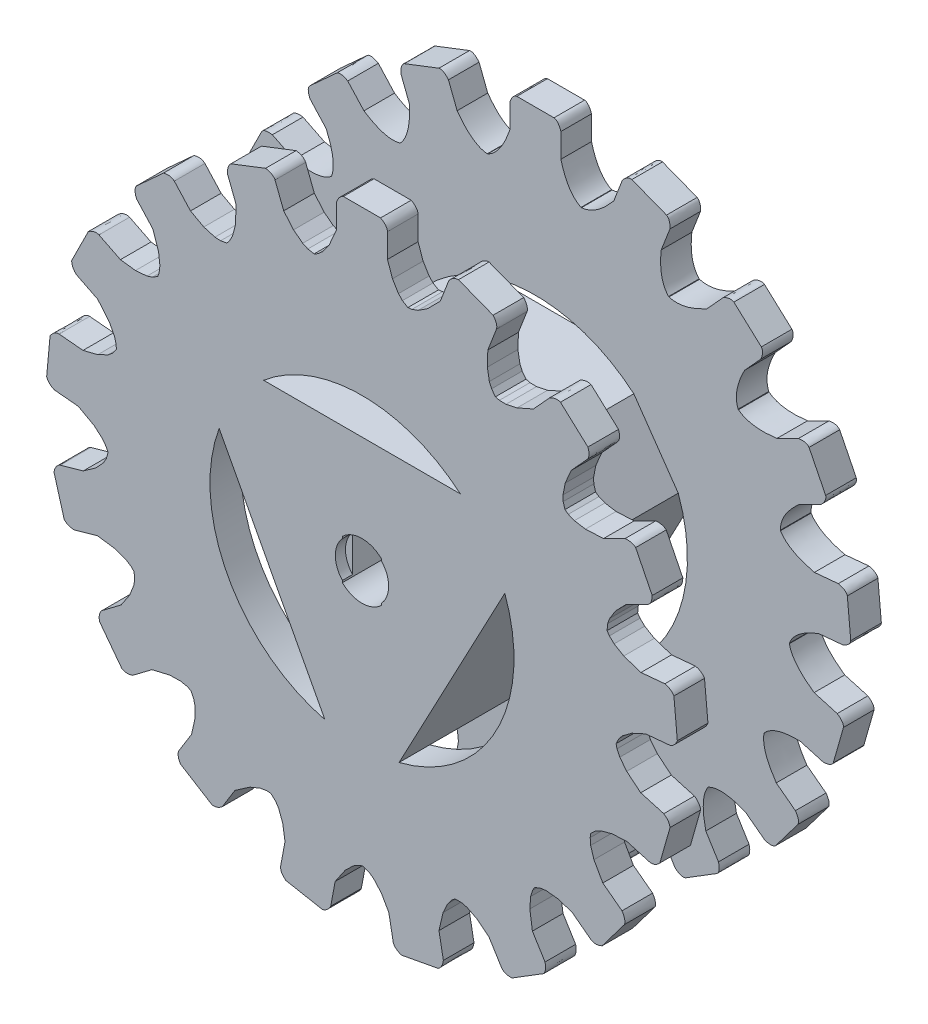
SolidWorks part; units mm, degrees
ref_plane "Front Plane" through (0, 0, 0) normal (0, 0, 1) x (1, 0, 0)
ref_plane "Top Plane" through (0, 0, 0) normal (0, 1, 0) x (1, 0, 0)
ref_plane "Right Plane" through (0, 0, 0) normal (1, 0, 0) x (0, 0, -1)
sketch "Sketch1" plane through (0, 0, 0) normal (0, 0, 1) x (1, 0, 0)
  line L0 (8.5238, 28.923) -> (7.6731, 26.7272)
  line L1 (-1.8223, 30.8747) -> (1.8223, 30.8747)
  line L2 (-2.5, 30.049) -> (-2.5, 27.6942)
  line L4 (2.5, 30.049) -> (2.5, 27.6942)
  line L5 (9.4539, 29.4481) -> (12.8525, 28.1315)
  line L6 (13.1861, 27.1167) -> (12.3355, 24.921)
  line L7 (18.3964, 23.8907) -> (16.8099, 22.1505)
  line L8 (19.4534, 24.0444) -> (22.1469, 21.589)
  line L9 (22.0914, 20.5222) -> (20.505, 18.782)
  line L10 (25.7844, 15.6319) -> (23.6765, 14.5823)
  line L11 (26.8256, 15.3933) -> (28.4502, 12.1307)
  line L12 (28.0131, 11.1561) -> (25.9052, 10.1065)
  line L13 (29.6901, 5.2619) -> (27.3454, 5.0446)
  line L14 (30.5748, 4.6633) -> (30.9111, 1.0342)
  line L15 (30.1515, 0.2832) -> (27.8067, 0.066)
  line L16 (29.5861, -5.8187) -> (27.3211, -5.1743)
  line L17 (30.1948, -6.6965) -> (29.1974, -10.202)
  line L18 (28.2177, -10.6279) -> (25.9528, -9.9834)
  line L19 (25.4862, -16.1135) -> (23.607, -14.6944)
  line L20 (25.7367, -17.1519) -> (23.5403, -20.0604)
  line L21 (22.473, -20.1036) -> (20.5939, -18.6845)
  line L22 (17.9443, -24.2321) -> (16.7047, -22.23)
  line L23 (17.8028, -25.2908) -> (14.704, -27.2095)
  line L24 (13.6932, -26.8643) -> (12.4536, -24.8622)
  line L25 (7.9789, -29.078) -> (7.5462, -26.7633)
  line L26 (7.4645, -30.0141) -> (3.8819, -30.6838)
  line L27 (3.0641, -29.9967) -> (2.6314, -27.682)
  line L28 (-3.0641, -29.9967) -> (-2.6314, -27.682)
  line L29 (-3.8819, -30.6838) -> (-7.4645, -30.0141)
  line L30 (-7.9789, -29.078) -> (-7.5462, -26.7633)
  line L31 (-13.6932, -26.8643) -> (-12.4536, -24.8622)
  line L32 (-14.704, -27.2095) -> (-17.8028, -25.2908)
  line L33 (-17.9443, -24.2321) -> (-16.7047, -22.23)
  line L34 (-22.473, -20.1036) -> (-20.5939, -18.6845)
  line L35 (-23.5403, -20.0604) -> (-25.7367, -17.1519)
  line L36 (-25.4862, -16.1135) -> (-23.607, -14.6944)
  line L37 (-28.2177, -10.6279) -> (-25.9528, -9.9834)
  line L38 (-29.1974, -10.202) -> (-30.1948, -6.6965)
  line L39 (-29.5861, -5.8187) -> (-27.3211, -5.1743)
  line L40 (-30.1515, 0.2832) -> (-27.8067, 0.066)
  line L41 (-30.9111, 1.0342) -> (-30.5748, 4.6633)
  line L42 (-29.6901, 5.2619) -> (-27.3454, 5.0446)
  line L43 (-28.0131, 11.1561) -> (-25.9052, 10.1065)
  line L44 (-28.4502, 12.1307) -> (-26.8256, 15.3933)
  line L45 (-25.7844, 15.6319) -> (-23.6765, 14.5823)
  line L46 (-22.0914, 20.5222) -> (-20.505, 18.782)
  line L47 (-22.1469, 21.589) -> (-19.4534, 24.0444)
  line L48 (-18.3964, 23.8907) -> (-16.8099, 22.1505)
  line L49 (-13.1861, 27.1167) -> (-12.3355, 24.921)
  line L50 (-12.8525, 28.1315) -> (-9.4539, 29.4481)
  line L51 (-8.5238, 28.923) -> (-7.6731, 26.7272)
  line L52 (3.6345, -14.4507) -> (14.0017, 5.0974)
  line L55 (-9.6443, 11.3587) -> (9.6443, 11.3587)
  line L59 (-14.0017, 5.0974) -> (-3.6345, -14.4507)
  arc A0 (-4.6728, 24.5594) -> (-4.7171, 24.5509) centre (0, 0) ccw
  arc A1 (-13.2291, 21.213) -> (-13.2674, 21.1891) centre (0, 0) ccw
  arc A2 (4.5146, 24.589) -> (4.4702, 24.5971) centre (0, 0) ccw
  arc A3 (13.0923, 21.2977) -> (13.0539, 21.3213) centre (0, 0) ccw
  arc A4 (19.9018, 15.13) -> (19.8745, 15.1659) centre (0, 0) ccw
  arc A5 (-19.9988, 15.0016) -> (-20.0259, 14.9655) centre (0, 0) ccw
  arc A6 (-24.0675, 6.7642) -> (-24.0797, 6.7207) centre (0, 0) ccw
  arc A7 (-24.8858, -2.3868) -> (-24.8815, -2.4317) centre (0, 0) ccw
  arc A8 (24.0235, 6.9189) -> (24.011, 6.9623) centre (0, 0) ccw
  arc A9 (24.9006, -2.2266) -> (24.9046, -2.1816) centre (0, 0) ccw
  arc A10 (22.4148, -11.0714) -> (22.4348, -11.0309) centre (0, 0) ccw
  arc A11 (16.9018, -18.4209) -> (16.935, -18.3904) centre (0, 0) ccw
  arc A12 (9.106, -23.2826) -> (9.148, -23.2662) centre (0, 0) ccw
  arc A13 (0.0804, -24.9999) -> (0.1256, -24.9997) centre (0, 0) ccw
  arc A14 (-8.956, -23.3407) -> (-8.9138, -23.3569) centre (0, 0) ccw
  arc A15 (-16.7829, -18.5293) -> (-16.7494, -18.5596) centre (0, 0) ccw
  arc A16 (-22.3431, -11.2154) -> (-22.3228, -11.2557) centre (0, 0) ccw
  arc A17 (3.6345, -14.4507) -> (14.0017, 5.0974) centre (0, 0) ccw
  arc A18 (-14.0017, 5.0974) -> (-3.6345, -14.4507) centre (0, 0) ccw
  arc A19 (9.6443, 11.3587) -> (-9.6443, 11.3587) centre (0, 0) ccw
  spline S0 degree 2 poles (-2.5, 27.6942) (-3.35, 25.1957) (-4.6728, 24.5594) knots 0 0 0 0.372776 0.372776 0.372776
  spline S1 degree 2 poles (2.5, 27.6942) (3.1474, 25.2334) (4.4702, 24.5971) knots 0 0 0 0.372776 0.372776 0.372776
  spline S2 degree 2 poles (-2.5, 30.049) (-2.2586, 30.7921) (-1.8223, 30.8747) knots 0 0 0 0.573783 0.573783 0.573783
  spline S3 degree 2 poles (2.5, 30.049) (2.2586, 30.7921) (1.8223, 30.8747) knots 0 0 0 0.573783 0.573783 0.573783
  spline S4 degree 2 poles (7.6731, 26.7272) (5.978, 24.7045) (4.5146, 24.589) knots 0 0 0 0.372776 0.372776 0.372776
  spline S5 degree 2 poles (8.5238, 28.923) (9.0173, 29.5287) (9.4539, 29.4481) knots 0 0 0 0.573783 0.573783 0.573783
  spline S6 degree 2 poles (13.1861, 27.1167) (13.2295, 27.8968) (12.8525, 28.1315) knots 0 0 0 0.573783 0.573783 0.573783
  spline S7 degree 2 poles (12.3355, 24.921) (12.0503, 22.3924) (13.0539, 21.3213) knots 0 0 0 0.372776 0.372776 0.372776
  spline S8 degree 2 poles (16.8099, 22.1505) (14.4986, 20.8767) (13.0923, 21.2977) knots 0 0 0 0.372776 0.372776 0.372776
  spline S9 degree 2 poles (18.3964, 23.8907) (19.0753, 24.2773) (19.4534, 24.0444) knots 0 0 0 0.573783 0.573783 0.573783
  spline S10 degree 2 poles (22.0914, 20.5222) (22.4136, 21.234) (22.1469, 21.589) knots 0 0 0 0.573783 0.573783 0.573783
  spline S11 degree 2 poles (20.505, 18.782) (19.3256, 16.5273) (19.8745, 15.1659) knots 0 0 0 0.372776 0.372776 0.372776
  spline S12 degree 2 poles (23.6765, 14.5823) (21.0611, 14.2295) (19.9018, 15.13) knots 0 0 0 0.372776 0.372776 0.372776
  spline S13 degree 2 poles (25.7844, 15.6319) (26.5572, 15.7471) (26.8256, 15.3933) knots 0 0 0 0.573783 0.573783 0.573783
  spline S14 degree 2 poles (28.0131, 11.1561) (28.5707, 11.7034) (28.4502, 12.1307) knots 0 0 0 0.573783 0.573783 0.573783
  spline S15 degree 2 poles (25.9052, 10.1065) (23.9909, 8.43) (24.011, 6.9623) knots 0 0 0 0.372776 0.372776 0.372776
  spline S16 degree 2 poles (27.3454, 5.0446) (24.7791, 5.6605) (24.0235, 6.9189) knots 0 0 0 0.372776 0.372776 0.372776
  spline S17 degree 2 poles (29.6901, 5.2619) (30.4523, 5.0901) (30.5748, 4.6633) knots 0 0 0 0.573783 0.573783 0.573783
  spline S18 degree 2 poles (30.1515, 0.2832) (30.8691, 0.5921) (30.9111, 1.0342) knots 0 0 0 0.573783 0.573783 0.573783
  spline S19 degree 2 poles (27.8067, 0.066) (25.4161, -0.8058) (24.9046, -2.1816) knots 0 0 0 0.372776 0.372776 0.372776
  spline S20 degree 2 poles (27.3211, -5.1743) (25.1506, -3.673) (24.9006, -2.2266) knots 0 0 0 0.372776 0.372776 0.372776
  spline S21 degree 2 poles (29.5861, -5.8187) (30.2347, -6.2542) (30.1948, -6.6965) knots 0 0 0 0.573783 0.573783 0.573783
  spline S22 degree 2 poles (28.2177, -10.6279) (28.9985, -10.5991) (29.1974, -10.202) knots 0 0 0 0.573783 0.573783 0.573783
  spline S23 degree 2 poles (25.9528, -9.9834) (23.4088, -9.9327) (22.4348, -11.0309) knots 0 0 0 0.372776 0.372776 0.372776
  spline S24 degree 2 poles (23.607, -14.6944) (22.1254, -12.5105) (22.4148, -11.0714) knots 0 0 0 0.372776 0.372776 0.372776
  spline S25 degree 2 poles (25.4862, -16.1135) (25.9337, -16.7539) (25.7367, -17.1519) knots 0 0 0 0.573783 0.573783 0.573783
  spline S26 degree 2 poles (22.473, -20.1036) (23.2115, -20.3588) (23.5403, -20.0604) knots 0 0 0 0.573783 0.573783 0.573783
  spline S27 degree 2 poles (20.5939, -18.6845) (18.2399, -17.7182) (16.935, -18.3904) knots 0 0 0 0.372776 0.372776 0.372776
  spline S28 degree 2 poles (16.7047, -22.23) (16.112, -19.6583) (16.9018, -18.4209) knots 0 0 0 0.372776 0.372776 0.372776
  spline S29 degree 2 poles (17.9443, -24.2321) (18.1303, -24.9909) (17.8028, -25.2908) knots 0 0 0 0.573783 0.573783 0.573783
  spline S30 degree 2 poles (13.6932, -26.8643) (14.2896, -27.369) (14.704, -27.2095) knots 0 0 0 0.573783 0.573783 0.573783
  spline S31 degree 2 poles (12.4536, -24.8622) (10.6077, -23.1108) (9.148, -23.2662) knots 0 0 0 0.372776 0.372776 0.372776
  spline S32 degree 2 poles (7.5462, -26.7633) (7.9226, -24.1511) (9.106, -23.2826) knots 0 0 0 0.372776 0.372776 0.372776
  spline S33 degree 2 poles (7.9789, -29.078) (7.8782, -29.8528) (7.4645, -30.0141) knots 0 0 0 0.573783 0.573783 0.573783
  spline S34 degree 2 poles (3.0641, -29.9967) (3.4378, -30.6828) (3.8819, -30.6838) knots 0 0 0 0.573783 0.573783 0.573783
  spline S35 degree 2 poles (2.6314, -27.682) (1.5428, -25.3821) (0.1256, -24.9997) knots 0 0 0 0.372776 0.372776 0.372776
  spline S36 degree 2 poles (-2.6314, -27.682) (-1.3367, -25.3823) (0.0804, -24.9999) knots 0 0 0 0.372776 0.372776 0.372776
  spline S37 degree 2 poles (-3.0641, -29.9967) (-3.4378, -30.6828) (-3.8819, -30.6838) knots 0 0 0 0.573783 0.573783 0.573783
  spline S38 degree 2 poles (-7.9789, -29.078) (-7.8782, -29.8528) (-7.4645, -30.0141) knots 0 0 0 0.573783 0.573783 0.573783
  spline S39 degree 2 poles (-7.5462, -26.7633) (-7.7305, -24.2254) (-8.9138, -23.3569) knots 0 0 0 0.372776 0.372776 0.372776
  spline S40 degree 2 poles (-12.4536, -24.8622) (-10.4156, -23.1854) (-8.956, -23.3407) knots 0 0 0 0.372776 0.372776 0.372776
  spline S41 degree 2 poles (-13.6932, -26.8643) (-14.2896, -27.369) (-14.704, -27.2095) knots 0 0 0 0.573783 0.573783 0.573783
  spline S42 degree 2 poles (-17.9443, -24.2321) (-18.1303, -24.9909) (-17.8028, -25.2908) knots 0 0 0 0.573783 0.573783 0.573783
  spline S43 degree 2 poles (-16.7047, -22.23) (-15.9597, -19.7969) (-16.7494, -18.5596) knots 0 0 0 0.372776 0.372776 0.372776
  spline S44 degree 2 poles (-20.5939, -18.6845) (-18.0878, -17.8572) (-16.7829, -18.5293) knots 0 0 0 0.372776 0.372776 0.372776
  spline S45 degree 2 poles (-22.473, -20.1036) (-23.2115, -20.3588) (-23.5403, -20.0604) knots 0 0 0 0.573783 0.573783 0.573783
  spline S46 degree 2 poles (-25.4862, -16.1135) (-25.9337, -16.7539) (-25.7367, -17.1519) knots 0 0 0 0.573783 0.573783 0.573783
  spline S47 degree 2 poles (-23.607, -14.6944) (-22.0334, -12.6948) (-22.3228, -11.2557) knots 0 0 0 0.372776 0.372776 0.372776
  spline S48 degree 2 poles (-25.9528, -9.9834) (-23.3171, -10.1172) (-22.3431, -11.2154) knots 0 0 0 0.372776 0.372776 0.372776
  spline S49 degree 2 poles (-28.2177, -10.6279) (-28.9985, -10.5991) (-29.1974, -10.202) knots 0 0 0 0.573783 0.573783 0.573783
  spline S50 degree 2 poles (-29.5861, -5.8187) (-30.2347, -6.2542) (-30.1948, -6.6965) knots 0 0 0 0.573783 0.573783 0.573783
  spline S51 degree 2 poles (-27.3211, -5.1743) (-25.1315, -3.8781) (-24.8815, -2.4317) knots 0 0 0 0.372776 0.372776 0.372776
  spline S52 degree 2 poles (-27.8067, 0.066) (-25.3973, -1.0109) (-24.8858, -2.3868) knots 0 0 0 0.372776 0.372776 0.372776
  spline S53 degree 2 poles (-30.1515, 0.2832) (-30.8691, 0.5921) (-30.9111, 1.0342) knots 0 0 0 0.573783 0.573783 0.573783
  spline S54 degree 2 poles (-29.6901, 5.2619) (-30.4523, 5.0901) (-30.5748, 4.6633) knots 0 0 0 0.573783 0.573783 0.573783
  spline S55 degree 2 poles (-27.3454, 5.0446) (-24.8353, 5.4623) (-24.0797, 6.7207) knots 0 0 0 0.372776 0.372776 0.372776
  spline S56 degree 2 poles (-25.9052, 10.1065) (-24.0475, 8.2319) (-24.0675, 6.7642) knots 0 0 0 0.372776 0.372776 0.372776
  spline S57 degree 2 poles (-28.0131, 11.1561) (-28.5707, 11.7034) (-28.4502, 12.1307) knots 0 0 0 0.573783 0.573783 0.573783
  spline S58 degree 2 poles (-25.7844, 15.6319) (-26.5572, 15.7471) (-26.8256, 15.3933) knots 0 0 0 0.573783 0.573783 0.573783
  spline S59 degree 2 poles (-23.6765, 14.5823) (-21.1851, 14.065) (-20.0259, 14.9655) knots 0 0 0 0.372776 0.372776 0.372776
  spline S60 degree 2 poles (-20.505, 18.782) (-19.4499, 16.363) (-19.9988, 15.0016) knots 0 0 0 0.372776 0.372776 0.372776
  spline S61 degree 2 poles (-22.0914, 20.5222) (-22.4136, 21.234) (-22.1469, 21.589) knots 0 0 0 0.573783 0.573783 0.573783
  spline S62 degree 2 poles (-18.3964, 23.8907) (-19.0753, 24.2773) (-19.4534, 24.0444) knots 0 0 0 0.573783 0.573783 0.573783
  spline S63 degree 2 poles (-16.8099, 22.1505) (-14.6736, 20.7681) (-13.2674, 21.1891) knots 0 0 0 0.372776 0.372776 0.372776
  spline S64 degree 2 poles (-12.3355, 24.921) (-12.2255, 22.2841) (-13.2291, 21.213) knots 0 0 0 0.372776 0.372776 0.372776
  spline S65 degree 2 poles (-13.1861, 27.1167) (-13.2295, 27.8968) (-12.8525, 28.1315) knots 0 0 0 0.573783 0.573783 0.573783
  spline S66 degree 2 poles (-8.5238, 28.923) (-9.0173, 29.5287) (-9.4539, 29.4481) knots 0 0 0 0.573783 0.573783 0.573783
  spline S67 degree 2 poles (-7.6731, 26.7272) (-6.1804, 24.6664) (-4.7171, 24.5509) knots 0 0 0 0.372776 0.372776 0.372776
  dimension "D1" = 50
  dimension "D2" = 17
extrude "Boss-Extrude2" add sketch "Sketch1" along normal blind 3
sketch "Sketch2" plane through (0, 0, 3) normal (0, 0, 1) x (1, 0, 0)
  line L0 (-14.0017, 5.0974) -> (-9.6443, 11.3587)
  line L1 (-9.6443, 11.3587) -> (9.6443, 11.3587)
  line L2 (9.6443, 11.3587) -> (14.0017, 5.0974)
  line L3 (14.0017, 5.0974) -> (3.6345, -14.4507)
  line L4 (3.6345, -14.4507) -> (-3.6345, -14.4507)
  line L5 (-3.6345, -14.4507) -> (-14.0017, 5.0974)
extrude "Boss-Extrude3" add sketch "Sketch2" along normal blind 14
sketch "Sketch3" plane through (0, 0, 17) normal (0, 0, 1) x (1, 0, 0)
  line L0 (-4.7171, 24.5509) -> (-4.3371, 24.7561)
  line L1 (-3.8537, 25.1795) -> (-3.2117, 26.0686)
  line L2 (-3.2117, 26.0686) -> (-2.5, 27.6942)
  line L3 (-2.5, 27.6942) -> (-2.5, 30.049)
  line L4 (-4.3371, 24.7561) -> (-3.8537, 25.1795)
  line L5 (-1.8223, 30.8747) -> (1.8223, 30.8747)
  line L6 (-0.1403, 24.7561) -> (-0.1403, 24.9932)
  line L7 (2.5, 30.049) -> (2.5, 27.6942)
  line L8 (2.5, 27.6942) -> (2.9903, 26.2914)
  line L9 (2.9903, 26.2914) -> (3.5787, 25.324)
  line L10 (3.9672, 24.9254) -> (4.5146, 24.589)
  line L11 (3.5787, 25.324) -> (3.9672, 24.9254)
  line L12 (1.8223, 30.8747) -> (-1.8223, 30.8747) construction
  line L13 (4.4702, 24.5971) -> (4.8987, 24.6512)
  line L14 (5.5024, 24.8713) -> (6.4222, 25.4685)
  line L15 (6.4222, 25.4685) -> (7.6731, 26.7272)
  line L16 (7.6731, 26.7272) -> (8.5238, 28.923)
  line L17 (9.4539, 29.4481) -> (12.8525, 28.1315)
  line L18 (13.1861, 27.1167) -> (12.3355, 24.921)
  line L19 (12.3355, 24.921) -> (12.2859, 23.4358)
  line L20 (12.2859, 23.4358) -> (12.4851, 22.3211)
  line L21 (12.4851, 22.3211) -> (12.7034, 21.8091)
  line L22 (12.7034, 21.8091) -> (13.0923, 21.2977)
  line L23 (4.8987, 24.6512) -> (5.5024, 24.8713)
  line L24 (13.0539, 21.3213) -> (13.4729, 21.2169)
  line L25 (14.1154, 21.2041) -> (15.1888, 21.4287)
  line L26 (15.1888, 21.4287) -> (16.8099, 22.1505)
  line L27 (16.8099, 22.1505) -> (18.3964, 23.8907)
  line L28 (19.4534, 24.0444) -> (22.1469, 21.589)
  line L29 (22.0914, 20.5222) -> (20.505, 18.782)
  line L30 (20.505, 18.782) -> (19.9223, 17.415)
  line L31 (19.9223, 17.415) -> (19.7054, 16.3036)
  line L32 (19.7054, 16.3036) -> (19.7239, 15.7474)
  line L33 (19.7239, 15.7474) -> (19.9018, 15.13)
  line L34 (13.4729, 21.2169) -> (14.1154, 21.2041)
  line L35 (19.8745, 15.1659) -> (20.2276, 14.9172)
  line L36 (20.8221, 14.6732) -> (21.9041, 14.4948)
  line L37 (21.9041, 14.4948) -> (23.6765, 14.5823)
  line L38 (23.6765, 14.5823) -> (25.7844, 15.6319)
  line L39 (26.8256, 15.3933) -> (28.4502, 12.1307)
  line L40 (28.0131, 11.1561) -> (25.9052, 10.1065)
  line L41 (25.9052, 10.1065) -> (24.868, 9.0423)
  line L42 (24.868, 9.0423) -> (24.2643, 8.0843)
  line L43 (24.2643, 8.0843) -> (24.0806, 7.5589)
  line L44 (24.0806, 7.5589) -> (24.0235, 6.9189)
  line L45 (20.2276, 14.9172) -> (20.8221, 14.6732)
  line L46 (24.011, 6.9623) -> (24.2504, 6.6028)
  line L47 (24.7166, 6.1605) -> (25.6611, 5.6034)
  line L48 (25.6611, 5.6034) -> (27.3454, 5.0446)
  line L49 (27.3454, 5.0446) -> (29.6901, 5.2619)
  line L50 (30.5748, 4.6633) -> (30.9111, 1.0342)
  line L51 (30.1515, 0.2832) -> (27.8067, 0.066)
  line L52 (27.8067, 0.066) -> (26.4551, -0.5517)
  line L53 (26.4551, -0.5517) -> (25.5461, -1.2269)
  line L54 (25.5461, -1.2269) -> (25.1851, -1.6505)
  line L55 (25.1851, -1.6505) -> (24.9006, -2.2266)
  line L56 (24.2504, 6.6028) -> (24.7166, 6.1605)
  line L57 (24.9046, -2.1816) -> (24.998, -2.6033)
  line L58 (25.2729, -3.1841) -> (25.9524, -4.0449)
  line L59 (25.9524, -4.0449) -> (27.3211, -5.1743)
  line L60 (27.3211, -5.1743) -> (29.5861, -5.8187)
  line L61 (30.1948, -6.6965) -> (29.1974, -10.202)
  line L62 (28.2177, -10.6279) -> (25.9528, -9.9834)
  line L63 (25.9528, -9.9834) -> (24.4694, -10.0711)
  line L64 (24.4694, -10.0711) -> (23.3779, -10.3724)
  line L65 (23.3779, -10.3724) -> (22.8882, -10.6369)
  line L66 (22.8882, -10.6369) -> (22.4148, -11.0714)
  line L67 (24.998, -2.6033) -> (25.2729, -3.1841)
  line L68 (22.4348, -11.0309) -> (22.3695, -11.4578)
  line L69 (22.4161, -12.0988) -> (22.7387, -13.1468)
  line L70 (22.7387, -13.1468) -> (23.607, -14.6944)
  line L71 (23.607, -14.6944) -> (25.4862, -16.1135)
  line L72 (25.7367, -17.1519) -> (23.5403, -20.0604)
  line L73 (22.473, -20.1036) -> (20.5939, -18.6845)
  line L74 (20.5939, -18.6845) -> (19.1789, -18.2304)
  line L75 (19.1789, -18.2304) -> (18.0523, -18.117)
  line L76 (18.0523, -18.117) -> (17.5001, -18.1868)
  line L77 (17.5001, -18.1868) -> (16.9018, -18.4209)
  line L78 (22.3695, -11.4578) -> (22.4161, -12.0988)
  line L79 (16.935, -18.3904) -> (16.7199, -18.7649)
  line L80 (16.5318, -19.3794) -> (16.454, -20.4732)
  line L81 (16.454, -20.4732) -> (16.7047, -22.23)
  line L82 (16.7047, -22.23) -> (17.9443, -24.2321)
  line L83 (17.8028, -25.2908) -> (14.704, -27.2095)
  line L84 (13.6932, -26.8643) -> (12.4536, -24.8622)
  line L85 (12.4536, -24.8622) -> (11.2982, -23.9276)
  line L86 (11.2982, -23.9276) -> (10.2886, -23.4148)
  line L87 (10.2886, -23.4148) -> (9.7485, -23.2804)
  line L88 (9.7485, -23.2804) -> (9.106, -23.2826)
  line L89 (16.7199, -18.7649) -> (16.5318, -19.3794)
  line L90 (9.148, -23.2662) -> (8.8122, -23.5377)
  line L91 (8.4148, -24.0427) -> (7.9472, -25.0346)
  line L92 (7.9472, -25.0346) -> (7.5462, -26.7633)
  line L93 (7.5462, -26.7633) -> (7.9789, -29.078)
  line L94 (7.4645, -30.0141) -> (3.8819, -30.6838)
  line L95 (3.0641, -29.9967) -> (2.6314, -27.682)
  line L96 (2.6314, -27.682) -> (1.8916, -26.3932)
  line L97 (1.8916, -26.3932) -> (1.1355, -25.5504)
  line L98 (1.1355, -25.5504) -> (0.6804, -25.2299)
  line L99 (0.6804, -25.2299) -> (0.0804, -24.9999)
  line L100 (8.8122, -23.5377) -> (8.4148, -24.0427)
  line L101 (0.1256, -24.9997) -> (-0.2857, -25.1316)
  line L102 (-0.8387, -25.4589) -> (-1.633, -26.2149)
  line L103 (-1.633, -26.2149) -> (-2.6314, -27.682)
  line L104 (-2.6314, -27.682) -> (-3.0641, -29.9967)
  line L105 (-3.8819, -30.6838) -> (-7.4645, -30.0141)
  line L106 (-7.9789, -29.078) -> (-7.5462, -26.7633)
  line L107 (-7.5462, -26.7633) -> (-7.7704, -25.2943)
  line L108 (-7.7704, -25.2943) -> (-8.1711, -24.2352)
  line L109 (-8.1711, -24.2352) -> (-8.4797, -23.772)
  line L110 (-8.4797, -23.772) -> (-8.956, -23.3407)
  line L111 (-0.2857, -25.1316) -> (-0.8387, -25.4589)
  line L112 (-8.9138, -23.3569) -> (-9.3449, -23.3313)
  line L113 (-9.9789, -23.4368) -> (-10.9927, -23.8548)
  line L114 (-10.9927, -23.8548) -> (-12.4536, -24.8622)
  line L115 (-12.4536, -24.8622) -> (-13.6932, -26.8643)
  line L116 (-14.704, -27.2095) -> (-17.8028, -25.2908)
  line L117 (-17.9443, -24.2321) -> (-16.7047, -22.23)
  line L118 (-16.7047, -22.23) -> (-16.3831, -20.7792)
  line L119 (-16.3831, -20.7792) -> (-16.3741, -19.6469)
  line L120 (-16.3741, -19.6469) -> (-16.4945, -19.1035)
  line L121 (-16.4945, -19.1035) -> (-16.7829, -18.5293)
  line L122 (-9.3449, -23.3313) -> (-9.9789, -23.4368)
  line L123 (-16.7494, -18.5596) -> (-17.1421, -18.38)
  line L124 (-17.7713, -18.2494) -> (-18.8677, -18.2729)
  line L125 (-18.8677, -18.2729) -> (-20.5939, -18.6845)
  line L126 (-20.5939, -18.6845) -> (-22.473, -20.1036)
  line L127 (-23.5403, -20.0604) -> (-25.7367, -17.1519)
  line L128 (-25.4862, -16.1135) -> (-23.607, -14.6944)
  line L129 (-23.607, -14.6944) -> (-22.783, -13.4578)
  line L130 (-22.783, -13.4578) -> (-22.3656, -12.4052)
  line L131 (-22.3656, -12.4052) -> (-22.2817, -11.855)
  line L132 (-22.2817, -11.855) -> (-22.3431, -11.2154)
  line L133 (-17.1421, -18.38) -> (-17.7713, -18.2494)
  line L134 (-22.3228, -11.2557) -> (-22.6242, -10.9464)
  line L135 (-23.1637, -10.5973) -> (-24.1945, -10.2232)
  line L136 (-24.1945, -10.2232) -> (-25.9528, -9.9834)
  line L137 (-25.9528, -9.9834) -> (-28.2177, -10.6279)
  line L138 (-29.1974, -10.202) -> (-30.1948, -6.6965)
  line L139 (-29.5861, -5.8187) -> (-27.3211, -5.1743)
  line L140 (-27.3211, -5.1743) -> (-26.1061, -4.3188)
  line L141 (-26.1061, -4.3188) -> (-25.3366, -3.4881)
  line L142 (-25.3366, -3.4881) -> (-25.0595, -3.0054)
  line L143 (-25.0595, -3.0054) -> (-24.8858, -2.3868)
  line L144 (-22.6242, -10.9464) -> (-23.1637, -10.5973)
  line L145 (-24.8815, -2.4317) -> (-25.0507, -2.0344)
  line L146 (-25.4277, -1.514) -> (-26.2538, -0.7927)
  line L147 (-26.2538, -0.7927) -> (-27.8067, 0.066)
  line L148 (-27.8067, 0.066) -> (-30.1515, 0.2832)
  line L149 (-30.9111, 1.0342) -> (-30.5748, 4.6633)
  line L150 (-29.6901, 5.2619) -> (-27.3454, 5.0446)
  line L151 (-27.3454, 5.0446) -> (-25.9033, 5.4034)
  line L152 (-25.9033, 5.4034) -> (-24.8857, 5.9001)
  line L153 (-24.8857, 5.9001) -> (-24.453, 6.2501)
  line L154 (-24.453, 6.2501) -> (-24.0675, 6.7642)
  line L155 (-25.0507, -2.0344) -> (-25.4277, -1.514)
  line L156 (-24.0797, 6.7207) -> (-24.094, 7.1523)
  line L157 (-24.2575, 7.7738) -> (-24.7673, 8.7448)
  line L158 (-24.7673, 8.7448) -> (-25.9052, 10.1065)
  line L159 (-25.9052, 10.1065) -> (-28.0131, 11.1561)
  line L160 (-28.4502, 12.1307) -> (-26.8256, 15.3933)
  line L161 (-25.7844, 15.6319) -> (-23.6765, 14.5823)
  line L162 (-23.6765, 14.5823) -> (-22.2022, 14.3959)
  line L163 (-22.2022, 14.3959) -> (-21.0739, 14.4914)
  line L164 (-21.0739, 14.4914) -> (-20.5439, 14.6615)
  line L165 (-20.5439, 14.6615) -> (-19.9988, 15.0016)
  line L166 (-24.094, 7.1523) -> (-24.2575, 7.7738)
  line L167 (-20.0259, 14.9655) -> (-19.8833, 15.3731)
  line L168 (-19.8113, 16.0117) -> (-19.9358, 17.1012)
  line L169 (-19.9358, 17.1012) -> (-20.505, 18.782)
  line L170 (-20.505, 18.782) -> (-22.0914, 20.5222)
  line L171 (-22.1469, 21.589) -> (-19.4534, 24.0444)
  line L172 (-18.3964, 23.8907) -> (-16.8099, 22.1505)
  line L173 (-16.8099, 22.1505) -> (-15.5025, 21.4441)
  line L174 (-15.5025, 21.4441) -> (-14.4159, 21.1256)
  line L175 (-14.4159, 21.1256) -> (-13.8603, 21.0928)
  line L176 (-13.8603, 21.0928) -> (-13.2291, 21.213)
  line L177 (-19.8833, 15.3731) -> (-19.8113, 16.0117)
  line L178 (-13.2674, 21.1891) -> (-12.9872, 21.5177)
  line L179 (-12.6894, 22.0871) -> (-12.4119, 23.1481)
  line L180 (-12.4119, 23.1481) -> (-12.3355, 24.921)
  line L181 (-12.3355, 24.921) -> (-13.1861, 27.1167)
  line L182 (-12.8525, 28.1315) -> (-9.4539, 29.4481)
  line L183 (-8.5238, 28.923) -> (-7.6731, 26.7272)
  line L184 (-7.6731, 26.7272) -> (-6.7092, 25.5962)
  line L185 (-6.7092, 25.5962) -> (-5.811, 24.9067)
  line L186 (-5.811, 24.9067) -> (-5.3048, 24.6753)
  line L187 (-5.3048, 24.6753) -> (-4.6728, 24.5594)
  line L188 (-12.9872, 21.5177) -> (-12.6894, 22.0871)
  line L189 (-14.0017, 5.0974) -> (-3.6345, -14.4507)
  line L190 (-14.0017, 5.0974) -> (-3.6345, -14.4507) construction
  line L191 (-9.6443, 11.3587) -> (9.6443, 11.3587)
  line L192 (3.6345, -14.4507) -> (14.0017, 5.0974)
  line L193 (14.0017, 5.0974) -> (3.6345, -14.4507)
  line L194 (9.6443, 11.3587) -> (-9.6443, 11.3587)
  line L195 (-3.6345, -14.4507) -> (-14.0017, 5.0974)
  arc A1 (3.6345, -14.4507) -> (14.0017, 5.0974) centre (0, 0) ccw
  arc A2 (-14.0017, 5.0974) -> (-3.6345, -14.4507) centre (0, 0) ccw
  arc A3 (9.6443, 11.3587) -> (-9.6443, 11.3587) centre (0, 0) ccw
  parabola Q0 (-2.5, 27.6942) -> (-4.6728, 24.5594) focus (-5.3497, 25.4535) apex (-5.0846, 24.4093) construction
  parabola Q1 (-2.5, 27.6942) -> (-4.6728, 24.5594) focus (-5.3497, 25.4535) apex (-5.0846, 24.4093) construction
  parabola Q2 (-1.8223, 30.8747) -> (-2.5, 30.049) focus (-1.7974, 30.5894) apex (-1.8776, 30.8613) construction
  parabola Q3 (4.4702, 24.5971) -> (2.5, 27.6942) focus (5.0417, 25.5458) apex (4.6606, 24.5162) construction
  parabola Q4 (4.4702, 24.5971) -> (2.5, 27.6942) focus (5.0417, 25.5458) apex (4.6606, 24.5162) construction
  parabola Q5 (-2.5, 27.6942) -> (-4.6728, 24.5594) focus (-5.3497, 25.4535) apex (-5.0846, 24.4093) construction
  parabola Q6 (4.4702, 24.5971) -> (2.5, 27.6942) focus (5.0417, 25.5458) apex (4.6606, 24.5162) construction
  parabola Q7 (-1.8223, 30.8747) -> (-2.5, 30.049) focus (-1.7974, 30.5894) apex (-1.8776, 30.8613) construction
  spline S0 degree 2 poles (-2.5, 30.049) (-2.2893, 30.6779) (-1.8223, 30.8747) knots 0 0 0 0.746925 0.746925 0.746925
  spline S1 degree 2 poles (1.8223, 30.8747) (2.4442, 30.5419) (2.5, 30.049) knots 0 0 0 0.688261 0.688261 0.688261
  spline S2 degree 2 poles (8.5238, 28.923) (8.9474, 29.4333) (9.4539, 29.4481) knots 0 0 0 0.746925 0.746925 0.746925
  spline S3 degree 2 poles (12.8525, 28.1315) (13.3122, 27.5965) (13.1861, 27.1167) knots 0 0 0 0.688261 0.688261 0.688261
  spline S4 degree 2 poles (18.3964, 23.8907) (18.9757, 24.2136) (19.4534, 24.0444) knots 0 0 0 0.746925 0.746925 0.746925
  spline S5 degree 2 poles (22.1469, 21.589) (22.3822, 20.9241) (22.0914, 20.5222) knots 0 0 0 0.688261 0.688261 0.688261
  spline S6 degree 2 poles (25.7844, 15.6319) (26.4413, 15.7236) (26.8256, 15.3933) knots 0 0 0 0.746925 0.746925 0.746925
  spline S7 degree 2 poles (28.4502, 12.1307) (28.4295, 11.4257) (28.0131, 11.1561) knots 0 0 0 0.688261 0.688261 0.688261
  spline S8 degree 2 poles (29.6901, 5.2619) (30.3358, 5.1102) (30.5748, 4.6633) knots 0 0 0 0.746925 0.746925 0.746925
  spline S9 degree 2 poles (30.9111, 1.0342) (30.6371, 0.3843) (30.1515, 0.2832) knots 0 0 0 0.688261 0.688261 0.688261
  spline S10 degree 2 poles (29.5861, -5.8187) (30.1333, -6.1935) (30.1948, -6.6965) knots 0 0 0 0.746925 0.746925 0.746925
  spline S11 degree 2 poles (29.1974, -10.202) (28.7071, -10.7091) (28.2177, -10.6279) knots 0 0 0 0.688261 0.688261 0.688261
  spline S12 degree 2 poles (25.4862, -16.1135) (25.8611, -16.6606) (25.7367, -17.1519) knots 0 0 0 0.746925 0.746925 0.746925
  spline S13 degree 2 poles (23.5403, -20.0604) (22.9, -20.3561) (22.473, -20.1036) knots 0 0 0 0.688261 0.688261 0.688261
  spline S14 degree 2 poles (17.9443, -24.2321) (18.0963, -24.8777) (17.8028, -25.2908) knots 0 0 0 0.746925 0.746925 0.746925
  spline S15 degree 2 poles (14.704, -27.2095) (14.0001, -27.2539) (13.6932, -26.8643) knots 0 0 0 0.688261 0.688261 0.688261
  spline S16 degree 2 poles (7.9789, -29.078) (7.8874, -29.7349) (7.4645, -30.0141) knots 0 0 0 0.746925 0.746925 0.746925
  spline S17 degree 2 poles (3.8819, -30.6838) (3.2095, -30.471) (3.0641, -29.9967) knots 0 0 0 0.688261 0.688261 0.688261
  spline S18 degree 2 poles (-3.0641, -29.9967) (-3.3867, -30.5762) (-3.8819, -30.6838) knots 0 0 0 0.746925 0.746925 0.746925
  spline S19 degree 2 poles (-7.4645, -30.0141) (-8.0146, -29.5727) (-7.9789, -29.078) knots 0 0 0 0.688261 0.688261 0.688261
  spline S20 degree 2 poles (-13.6932, -26.8643) (-14.2034, -27.2881) (-14.704, -27.2095) knots 0 0 0 0.746925 0.746925 0.746925
  spline S21 degree 2 poles (-17.8028, -25.2908) (-18.1563, -24.6805) (-17.9443, -24.2321) knots 0 0 0 0.688261 0.688261 0.688261
  spline S22 degree 2 poles (-22.473, -20.1036) (-23.1019, -20.3145) (-23.5403, -20.0604) knots 0 0 0 0.746925 0.746925 0.746925
  spline S23 degree 2 poles (-25.7367, -17.1519) (-25.8459, -16.4551) (-25.4862, -16.1135) knots 0 0 0 0.688261 0.688261 0.688261
  spline S24 degree 2 poles (-28.2177, -10.6279) (-28.8803, -10.5973) (-29.1974, -10.202) knots 0 0 0 0.746925 0.746925 0.746925
  spline S25 degree 2 poles (-30.1948, -6.6965) (-30.0449, -6.0073) (-29.5861, -5.8187) knots 0 0 0 0.688261 0.688261 0.688261
  spline S26 degree 2 poles (-30.1515, 0.2832) (-30.7583, 0.551) (-30.9111, 1.0342) knots 0 0 0 0.746925 0.746925 0.746925
  spline S27 degree 2 poles (-30.5748, 4.6633) (-30.1861, 5.2518) (-29.6901, 5.2619) knots 0 0 0 0.688261 0.688261 0.688261
  spline S28 degree 2 poles (-28.0131, 11.1561) (-28.4822, 11.625) (-28.4502, 12.1307) knots 0 0 0 0.746925 0.746925 0.746925
  spline S29 degree 2 poles (-26.8256, 15.3933) (-26.2505, 15.8016) (-25.7844, 15.6319) knots 0 0 0 0.688261 0.688261 0.688261
  spline S30 degree 2 poles (-22.0914, 20.5222) (-22.3594, 21.1289) (-22.1469, 21.589) knots 0 0 0 0.746925 0.746925 0.746925
  spline S31 degree 2 poles (-19.4534, 24.0444) (-18.7697, 24.2174) (-18.3964, 23.8907) knots 0 0 0 0.688261 0.688261 0.688261
  spline S32 degree 2 poles (-13.1861, 27.1167) (-13.2169, 27.7793) (-12.8525, 28.1315) knots 0 0 0 0.746925 0.746925 0.746925
  spline S33 degree 2 poles (-9.4539, 29.4481) (-8.7539, 29.3624) (-8.5238, 28.923) knots 0 0 0 0.688261 0.688261 0.688261
  dimension "D1" = 17
extrude "Boss-Extrude7" add sketch "Sketch3" along normal blind 3
sketch "Sketch6" plane through (0, 0, 20) normal (0, 0, 1) x (1, 0, 0)
  line L10 (-1.9239, 1.965) -> (-1.9239, -1.965)
  line L12 (1.9239, 1.965) -> (1.9239, -1.965)
  circle A0 centre (0, 0) radius 2.75
  point P7 (1.6992, -2.1622)
  point P8 (-2.0291, -1.8561)
  dimension "D1" = 5.5
  dimension "D2" = 3.93
sketch "Sketch7" plane through (0, 0, 20) normal (0, 0, 1) x (1, 0, 0)
  circle A0 centre (0, 0) radius 2.616
sketch "Sketch8" plane through (0, 0, 0) normal (0, 0, -1) x (-1, 0, 0)
  line L1 (0, -5.9927) -> (5.1898, -2.9963)
  line L2 (5.1898, -2.9963) -> (5.1898, 2.9963)
  line L3 (5.1898, 2.9963) -> (0, 5.9927)
  line L4 (0, 5.9927) -> (-5.1898, 2.9963)
  line L5 (-5.1898, 2.9963) -> (-5.1898, -2.9963)
  line L6 (-5.1898, -2.9963) -> (0, -5.9927)
  circle A0 centre (0, 0) radius 5.1898 construction
extrude "Boss-Extrude10" add sketch "Sketch8" along normal blind 5
extrude "Cut-Extrude2" cut sketch "Sketch6" against normal blind 6.8 contours L12 A0 L10
extrude "Cut-Extrude3" cut sketch "Sketch7" against normal blind 1 contours A0
